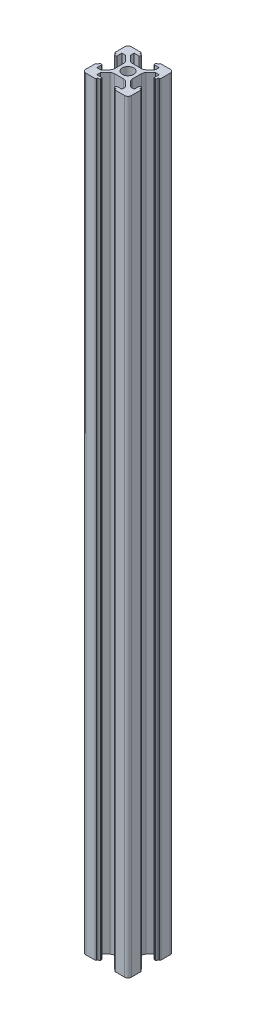
SolidWorks part; units mm, degrees
ref_plane "Front Plane" through (0, 0, 0) normal (0, 0, 1) x (1, 0, 0)
ref_plane "Top Plane" through (0, 0, 0) normal (0, 1, 0) x (1, 0, 0)
ref_plane "Right Plane" through (0, 0, 0) normal (1, 0, 0) x (0, 0, -1)
sketch "Sketch1" plane through (0, 0, 0) normal (0, 1, 0) x (1, 0, 0)
  line L0 (3.4251, 4.4858) -> (5.5, 6.5607)
  line L1 (-10, -10) -> (10, -10) construction
  line L2 (-10, -10) -> (-10, 10) construction
  line L3 (-10, 10) -> (10, 10) construction
  line L4 (10, -10) -> (10, 10) construction
  line L5 (-10, -10) -> (10, 10) construction
  line L6 (-10, 10) -> (10, -10) construction
  line L9 (0, 3.9) -> (2.0109, 3.9)
  line L10 (3.9, 0) -> (3.9, 2.0109)
  line L11 (3.9, 0) -> (3.9, -2.0109)
  line L12 (4.4858, -3.4251) -> (6.5607, -5.5)
  line L13 (4.4858, 3.4251) -> (6.5607, 5.5)
  line L14 (5.5, 8.2) -> (3.1, 8.2)
  line L15 (3.1, 8.2) -> (3.1, 9.24)
  line L16 (5.5, 8.2) -> (5.5, 6.5607)
  line L17 (8.2, 5.5) -> (6.5607, 5.5)
  line L21 (4.1, 10) -> (4.1, 9.24)
  line L22 (8.2, 5.5) -> (8.2, 3.1)
  line L23 (8.2, 3.1) -> (9.24, 3.1)
  line L24 (9.24, 3.1) -> (9.24, 4.1)
  line L25 (10, 4.1) -> (9.24, 4.1)
  line L26 (0, 0) -> (50000, 0) construction
  line L27 (0, 0) -> (0, -50000) construction
  line L28 (4.1, 10) -> (8.5, 10)
  line L29 (10, 8.5) -> (10, 4.1)
  line L30 (4.1, 9.24) -> (3.1, 9.24)
  line L31 (8.2, -5.5) -> (6.5607, -5.5)
  line L32 (8.2, -5.5) -> (8.2, -3.1)
  line L33 (8.2, -3.1) -> (9.24, -3.1)
  line L34 (9.24, -4.1) -> (9.24, -3.1)
  line L35 (10, -4.1) -> (9.24, -4.1)
  line L36 (10, -4.1) -> (10, -8.5)
  line L37 (8.5, -10) -> (4.1, -10)
  line L38 (4.1, -10) -> (4.1, -9.24)
  line L39 (3.1, -9.24) -> (4.1, -9.24)
  line L40 (3.1, -8.2) -> (3.1, -9.24)
  line L41 (5.5, -8.2) -> (3.1, -8.2)
  line L42 (5.5, -8.2) -> (5.5, -6.5607)
  line L43 (3.4251, -4.4858) -> (5.5, -6.5607)
  line L44 (0, -3.9) -> (2.0109, -3.9)
  line L45 (0, -3.9) -> (-2.0109, -3.9)
  line L46 (-3.4251, -4.4858) -> (-5.5, -6.5607)
  line L47 (-5.5, -8.2) -> (-5.5, -6.5607)
  line L48 (-5.5, -8.2) -> (-3.1, -8.2)
  line L49 (-3.1, -8.2) -> (-3.1, -9.24)
  line L50 (-4.1, -9.24) -> (-3.1, -9.24)
  line L51 (-4.1, -10) -> (-4.1, -9.24)
  line L52 (-4.1, -10) -> (-8.5, -10)
  line L53 (-10, -8.5) -> (-10, -4.1)
  line L54 (-10, -4.1) -> (-9.24, -4.1)
  line L55 (-9.24, -3.1) -> (-9.24, -4.1)
  line L56 (-8.2, -3.1) -> (-9.24, -3.1)
  line L57 (-8.2, -5.5) -> (-8.2, -3.1)
  line L58 (-8.2, -5.5) -> (-6.5607, -5.5)
  line L59 (-4.4858, -3.4251) -> (-6.5607, -5.5)
  line L60 (-3.9, 0) -> (-3.9, -2.0109)
  line L61 (-3.9, 0) -> (-3.9, 2.0109)
  line L62 (-4.4858, 3.4251) -> (-6.5607, 5.5)
  line L63 (-8.2, 5.5) -> (-6.5607, 5.5)
  line L64 (-8.2, 5.5) -> (-8.2, 3.1)
  line L65 (-8.2, 3.1) -> (-9.24, 3.1)
  line L66 (-9.24, 4.1) -> (-9.24, 3.1)
  line L67 (-10, 4.1) -> (-9.24, 4.1)
  line L68 (-10, 4.1) -> (-10, 8.5)
  line L69 (-8.5, 10) -> (-4.1, 10)
  line L70 (-4.1, 10) -> (-4.1, 9.24)
  line L71 (-3.1, 9.24) -> (-4.1, 9.24)
  line L72 (-3.1, 8.2) -> (-3.1, 9.24)
  line L73 (-5.5, 8.2) -> (-3.1, 8.2)
  line L74 (-5.5, 8.2) -> (-5.5, 6.5607)
  line L75 (-3.4251, 4.4858) -> (-5.5, 6.5607)
  line L76 (0, 3.9) -> (-2.0109, 3.9)
  arc A1 (3.9, 2.0109) -> (4.4858, 3.4251) centre (5.9, 2.0109) cw
  arc A2 (3.4251, 4.4858) -> (2.0109, 3.9) centre (2.0109, 5.9) cw
  arc A3 (10, 8.5) -> (8.5, 10) centre (8.5, 8.5) ccw
  arc A4 (2.5, 0) -> (0, 2.5) centre (0, 0) ccw
  arc A5 (0, -2.5) -> (2.5, 0) centre (0, 0) ccw
  arc A6 (4.4858, -3.4251) -> (3.9, -2.0109) centre (5.9, -2.0109) cw
  arc A7 (8.5, -10) -> (10, -8.5) centre (8.5, -8.5) ccw
  arc A8 (2.0109, -3.9) -> (3.4251, -4.4858) centre (2.0109, -5.9) cw
  arc A9 (-2.5, 0) -> (0, -2.5) centre (0, 0) ccw
  arc A10 (-3.4251, -4.4858) -> (-2.0109, -3.9) centre (-2.0109, -5.9) cw
  arc A11 (-10, -8.5) -> (-8.5, -10) centre (-8.5, -8.5) ccw
  arc A12 (-3.9, -2.0109) -> (-4.4858, -3.4251) centre (-5.9, -2.0109) cw
  arc A13 (0, 2.5) -> (-2.5, 0) centre (0, 0) ccw
  arc A14 (-4.4858, 3.4251) -> (-3.9, 2.0109) centre (-5.9, 2.0109) cw
  arc A15 (-8.5, 10) -> (-10, 8.5) centre (-8.5, 8.5) ccw
  arc A16 (-2.0109, 3.9) -> (-3.4251, 4.4858) centre (-2.0109, 5.9) cw
  point P0 (0, 0)
  point P30 (3.1, 10)
  point P115 (0, 0)
  dimension "D2" = 2.5
  dimension "D3" = 2
  dimension "D12" = 1.5
  dimension "D1" = 20
  dimension "D4" = 1.5
  dimension "D5" = 1.8
  dimension "D6" = 5.5
  dimension "D7" = 0.76
  dimension "D8" = 3.1
  dimension "D9" = 1
  dimension "D10" = 3.9
  dimension "D11" = 3.9
  dimension "D13" = 4
extrude "Boss-Extrude1" add sketch "Sketch1" along normal blind 335 contours L76 A16 L75 L74 L73 L72 L71 L70 L69 A15 L68 L67 L66 L65 L64 L63 L62 A14 L61 L60 A12 L59 L58 L57 L56 L55 L54 L53 A11 L52 L51 L50 L49 L48 L47 L46 A10 L45 L44 A8 L43 L42 L41 L40 L39 L38 L37 A7 L36 L35 L34
fillet "Fillet1" radius 0.35 33 edges at (-4.1, 167.5, -10) (-4.1, 167.5, -9.24) (-3.1, 167.5, -9.24) (-3.1, 167.5, -8.2) (-9.24, 167.5, -4.1) (-10, 167.5, -4.1) (-9.24, 167.5, -3.1) (-8.2, 167.5, -3.1) (-10, 167.5, 4.1) (-9.24, 167.5, 4.1) (-9.24, 167.5, 3.1) (-8.2, 167.5, 3.1) (-4.1, 167.5, 10) (-4.1, 167.5, 9.24) (-3.1, 167.5, 9.24) (-3.1, 167.5, 8.2) (4.1, 167.5, 10) (4.1, 167.5, 9.24) (3.1, 167.5, 9.24) (3.1, 167.5, 8.2) (10, 167.5, 4.1) (9.24, 167.5, 4.1) (9.24, 167.5, 3.1) (8.2, 167.5, 3.1) (10, 167.5, -4.1) (9.24, 167.5, -4.1) (9.24, 167.5, -3.1) (8.2, 167.5, -3.1) (3.1, 167.5, -8.2) (4.1, 167.5, -10) (5.5, 167.5, -6.5607) (3.1, 167.5, -9.24) (4.1, 167.5, -9.24)
